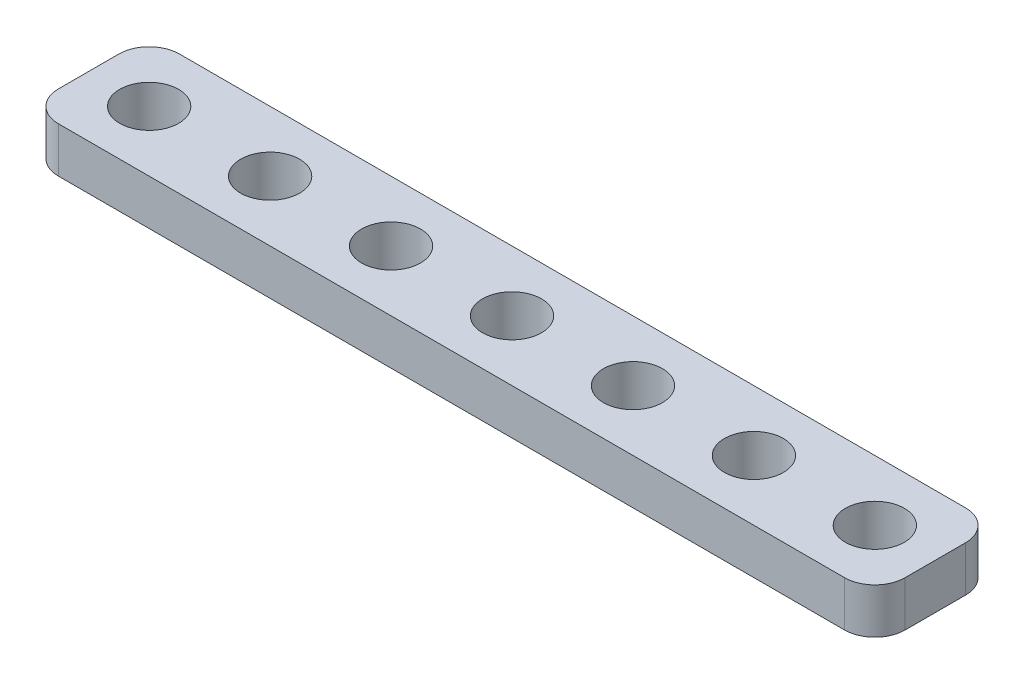
SolidWorks part; units mm, degrees
ref_plane "Front Plane" through (0, 0, 0) normal (0, 0, 1) x (1, 0, 0)
ref_plane "Top Plane" through (0, 0, 0) normal (0, 1, 0) x (1, 0, 0)
ref_plane "Right Plane" through (0, 0, 0) normal (1, 0, 0) x (0, 0, -1)
sketch "Sketch1" plane through (0, 0, 0) normal (0, 1, 0) x (1, 0, 0)
  line L1 (2, 0) -> (54, 0)
  line L2 (0, -2) -> (0, -6)
  line L3 (2, -8) -> (54, -8)
  line L4 (56, -2) -> (56, -6)
  arc A0 (54, -8) -> (56, -6) centre (54, -6) ccw
  arc A1 (0, -6) -> (2, -8) centre (2, -6) ccw
  arc A2 (2, 0) -> (0, -2) centre (2, -2) ccw
  arc A3 (54, 0) -> (56, -2) centre (54, -2) cw
  point P7 (56, -8)
  point P12 (0, 0)
  point P15 (56, 0)
  dimension "D3" = 2
  dimension "D1" = 56
  dimension "D2" = 8
extrude "Boss-Extrude1" add sketch "Sketch1" along normal blind 3
sketch "Sketch2" plane through (0, 3, 0) normal (0, 1, 0) x (1, 0, 0)
  line L0 (54, 0) -> (2, 0) construction
  line L1 (56, -6) -> (56, -2) construction
  line L2 (52, -4) -> (0, -4) construction
  line L3 (0, -2) -> (0, -6) construction
  circle A0 centre (52, -4) radius 1.95
  circle A1 centre (44, -4) radius 1.95
  circle A3 centre (-12, -4) radius 1.95
  circle A4 centre (-4, -4) radius 1.95
  circle A5 centre (4, -4) radius 1.95
  circle A6 centre (12, -4) radius 1.95
  circle A7 centre (20, -4) radius 1.95
  circle A8 centre (28, -4) radius 1.95
  circle A9 centre (36, -4) radius 1.95
  dimension "D1" = 3.9
  dimension "D4" = 3.9
  dimension "D8" = 3.9
  dimension "D9" = 3.9
  dimension "D10" = 3.9
  dimension "D11" = 3.9
  dimension "D12" = 3.9
  dimension "D13" = 3.9
  dimension "D14" = 3.9
  dimension "D2" = 4
  dimension "D3" = 4
  dimension "D5" = 8
  dimension "D15" = 8
  dimension "D16" = 8
  dimension "D17" = 8
  dimension "D18" = 8
  dimension "D19" = 8
  dimension "D20" = 8
  dimension "D21" = 8
extrude "Cut-Extrude1" cut sketch "Sketch2" against normal through all
